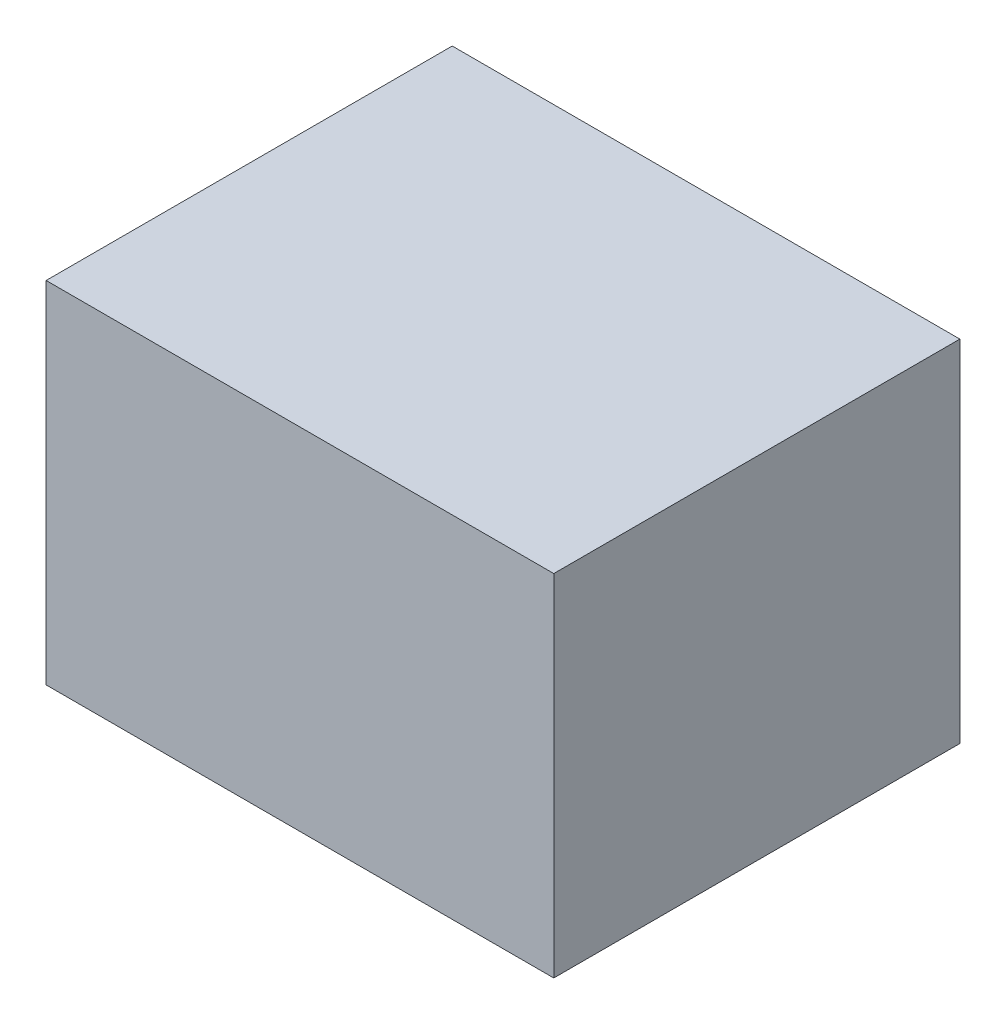
SolidWorks part; units mm, degrees
ref_plane "Front Plane" through (0, 0, 0) normal (0, 0, 1) x (1, 0, 0)
ref_plane "Top Plane" through (0, 0, 0) normal (0, 1, 0) x (1, 0, 0)
ref_plane "Right Plane" through (0, 0, 0) normal (1, 0, 0) x (0, 0, -1)
sketch "Sketch1" plane through (0, 0, 0) normal (0, 1, 0) x (1, 0, 0)
  line L1 (0, 0) -> (-38.1, 0)
  line L2 (0, 0) -> (0, 30.48)
  line L3 (0, 30.48) -> (-38.1, 30.48)
  line L4 (-38.1, 0) -> (-38.1, 30.48)
  line L5 (0, 0) -> (-38.1, 30.48) construction
  line L6 (0, 30.48) -> (-38.1, 0) construction
  point P4 (-19.05, 15.24)
  dimension "D1" = 38.1
  dimension "D2" = 30.48
extrude "Boss-Extrude1" add sketch "Sketch1" along normal blind 26.289
